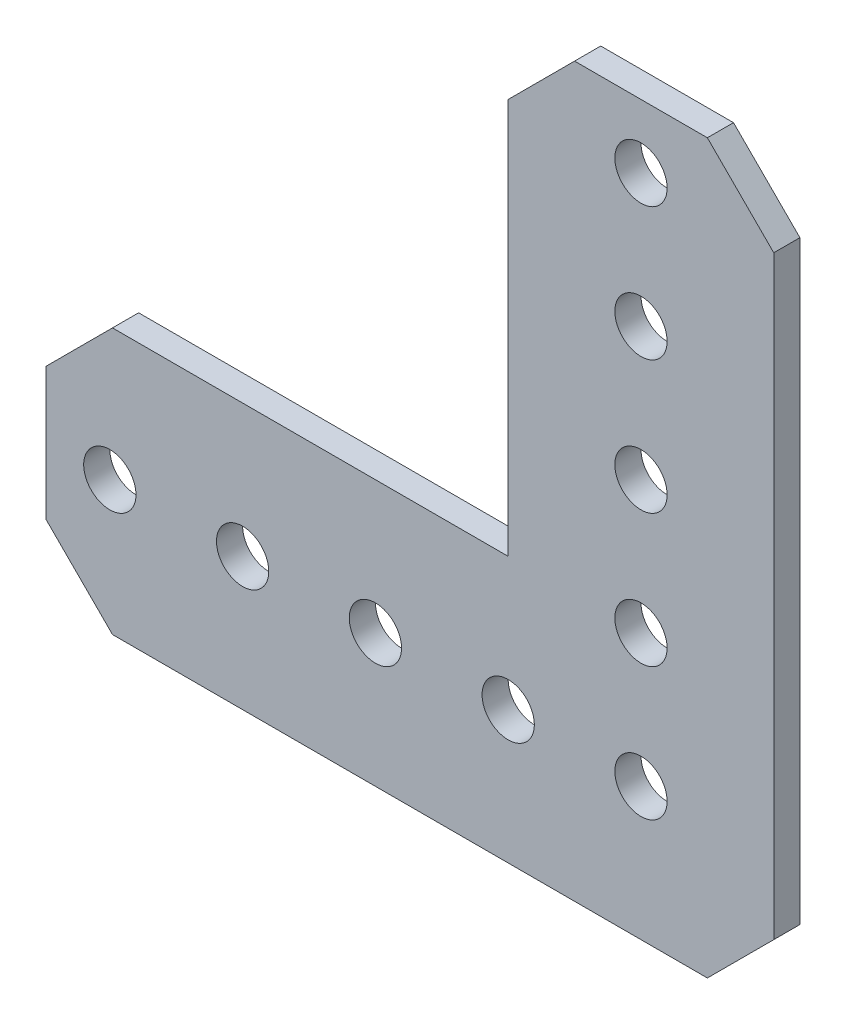
SolidWorks part; units mm, degrees
material "5052-H32"
ref_plane "Front Plane" through (0, 0, 0) normal (0, 0, 1) x (1, 0, 0)
ref_plane "Top Plane" through (0, 0, 0) normal (0, 1, 0) x (1, 0, 0)
ref_plane "Right Plane" through (0, 0, 0) normal (1, 0, 0) x (0, 0, -1)
ref_plane "Plane1" through (0, 0, -1.25) normal (0, 0, -1) x (-1, 0, 0)
sketch "Sketch1" plane through (0, 0, -1.25) normal (0, 0, -1) x (-1, 0, 0)
  line L0 (-6.35, -12.7) -> (50.546, -12.7)
  line L1 (50.546, -12.7) -> (56.896, -6.35)
  line L2 (56.896, -6.35) -> (56.896, 6.35)
  line L3 (56.896, 6.35) -> (50.546, 12.7)
  line L4 (50.546, 12.7) -> (12.7, 12.7)
  line L5 (12.7, 12.7) -> (12.7, 50.546)
  line L6 (12.7, 50.546) -> (6.35, 56.896)
  line L7 (6.35, 56.896) -> (-6.35, 56.896)
  line L8 (-6.35, 56.896) -> (-12.7, 50.546)
  line L9 (-12.7, 50.546) -> (-12.7, -6.35)
  line L10 (-12.7, -6.35) -> (-6.35, -12.7)
  circle A0 centre (0, 12.7) radius 2.5
  circle A1 centre (0, 25.4) radius 2.5
  circle A2 centre (12.7, 0) radius 2.5
  circle A3 centre (25.4, 0) radius 2.5
  circle A4 centre (0, 0) radius 2.5
  circle A5 centre (50.8, 0) radius 2.5
  circle A6 centre (38.1, 0) radius 2.5
  circle A7 centre (0, 50.8) radius 2.5
  circle A8 centre (0, 38.1) radius 2.5
extrude "Boss-Extrude1" add sketch "Sketch1" against normal blind 2.5
